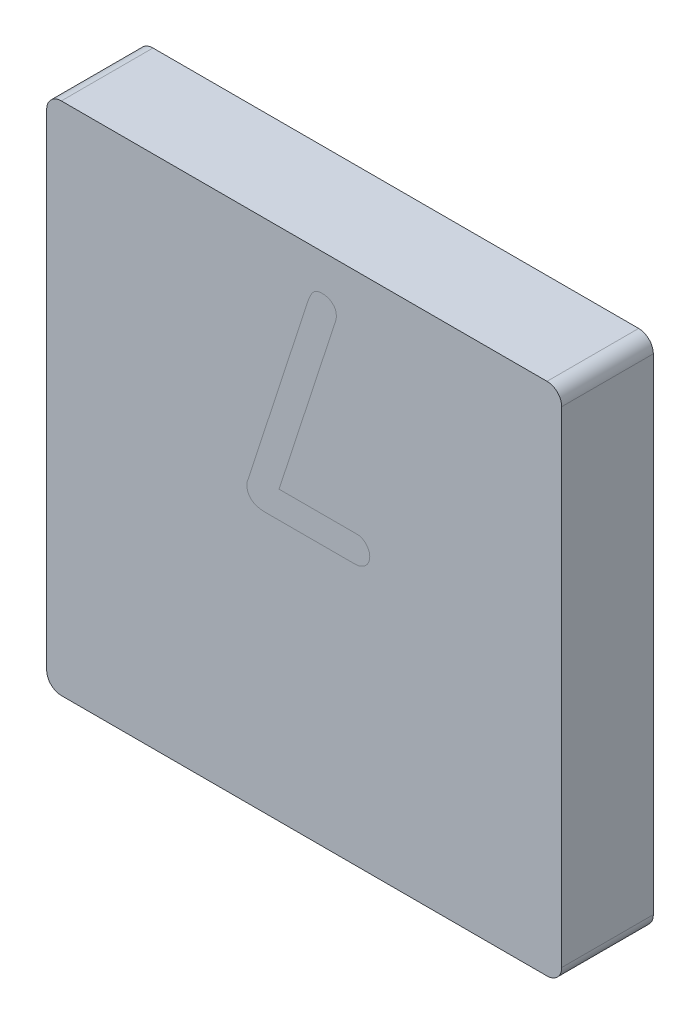
SolidWorks part; units mm, degrees
material "Nylon 101"
ref_plane "Front Plane" through (0, 0, 0) normal (0, 0, 1) x (1, 0, 0)
ref_plane "Top Plane" through (0, 0, 0) normal (0, 1, 0) x (1, 0, 0)
ref_plane "Right Plane" through (0, 0, 0) normal (1, 0, 0) x (0, 0, -1)
sketch "Sketch1" plane through (0, 0, 0) normal (0, 0, 1) x (1, 0, 0)
  line L0 (4.207, 4.715) -> (-4.207, 4.715) construction
  line L1 (4.715, -4.207) -> (4.715, 4.207) construction
  line L2 (-4.207, -4.715) -> (4.207, -4.715) construction
  line L3 (-4.715, 4.207) -> (-4.715, -4.207) construction
  line L4 (4.207, 4.715) -> (-4.207, 4.715) construction
  line L5 (4.715, -4.207) -> (4.715, 4.207) construction
  line L6 (-4.207, -4.715) -> (4.207, -4.715) construction
  line L7 (-4.715, 4.207) -> (-4.715, -4.207) construction
  line L8 (4.207, 4.461) -> (-4.207, 4.461)
  line L9 (-4.461, 4.207) -> (-4.461, -4.207)
  line L10 (-4.207, -4.461) -> (4.207, -4.461)
  line L11 (4.461, -4.207) -> (4.461, 4.207)
  arc A0 (4.715, 4.207) -> (4.207, 4.715) centre (4.207, 4.207) ccw construction
  arc A1 (4.207, -4.715) -> (4.715, -4.207) centre (4.207, -4.207) ccw construction
  arc A2 (-4.715, -4.207) -> (-4.207, -4.715) centre (-4.207, -4.207) ccw construction
  arc A3 (-4.207, 4.715) -> (-4.715, 4.207) centre (-4.207, 4.207) ccw construction
  arc A4 (4.715, 4.207) -> (4.207, 4.715) centre (4.207, 4.207) ccw construction
  arc A5 (4.207, -4.715) -> (4.715, -4.207) centre (4.207, -4.207) ccw construction
  arc A6 (-4.715, -4.207) -> (-4.207, -4.715) centre (-4.207, -4.207) ccw construction
  arc A7 (-4.207, 4.715) -> (-4.715, 4.207) centre (-4.207, 4.207) ccw construction
  arc A8 (-4.207, 4.461) -> (-4.461, 4.207) centre (-4.207, 4.207) ccw
  arc A9 (-4.461, -4.207) -> (-4.207, -4.461) centre (-4.207, -4.207) ccw
  arc A10 (4.207, -4.461) -> (4.461, -4.207) centre (4.207, -4.207) ccw
  arc A11 (4.461, 4.207) -> (4.207, 4.461) centre (4.207, 4.207) ccw
  dimension "D1" = 0.254
extrude "Boss-Extrude1" add sketch "Sketch1" along normal blind 1.5875
sketch "Sketch2" plane through (0, 0, 1.5875) normal (0, 0, 1) x (1, 0, 0)
  line L0 (4.461, 3.8355) -> (-4.461, 3.8355) construction
  line L1 (4.461, -4.207) -> (4.461, 4.207) construction
  line L2 (-4.461, 4.207) -> (-4.461, -4.207) construction
  text T0 "7" font "GordonURWMed" height in points 16
sketch "Sketch4" plane through (0, 0, 1.5875) normal (0, 0, 1) x (1, 0, 0)
  line L0 (4.461, -0.7785) -> (-4.461, -0.7785) construction
  line L1 (4.461, -4.207) -> (4.461, 4.207) construction
  line L2 (-4.461, 4.207) -> (-4.461, -4.207) construction
  text T0 "N" font "GordonURWMed" height in points 12
wrap "Direction" [suppressed] sketch "Sketch4" source sketch "Sketch4"
split line "Number"
sketch "Sketch5" [suppressed] plane through (0, 0, 1.5875) normal (0, 0, 1) x (1, 0, 0)
  line L0 (4.461, 0) -> (-4.461, 0) construction
  line L1 (4.461, -4.207) -> (4.461, 4.207) construction
  line L2 (-4.461, 4.207) -> (-4.461, -4.207) construction
  line L3 (4.461, 1.651) -> (-4.461, 1.651) construction
  text T0 "CLR" font "GordonURWMed" height in points 14
  dimension "D1" = 1.651
wrap "CLR" [suppressed] sketch "Sketch5" source sketch "Sketch5"
sketch "Sketch6" [suppressed] plane through (0, 0, 1.5875) normal (0, 0, 1) x (1, 0, 0)
  line L0 (4.461, 0) -> (-4.461, 0) construction
  line L4 (4.461, 1.651) -> (-4.461, 1.651) construction
  text T0 "ENT" font "GordonURWCon" height in points 16
  dimension "D1" = 1.651
wrap "ENT" [suppressed] sketch "Sketch6" source sketch "Sketch6"
sketch "Sketch8" [suppressed] plane through (0, 0, 1.5875) normal (0, 0, 1) x (1, 0, 0)
  line L0 (4.461, 3.302) -> (-4.461, 3.302) construction
  line L3 (4.461, 0) -> (-4.461, 0) construction
  line L4 (4.461, -0.508) -> (-4.461, -0.508) construction
  text T0 "EM" font "GordonURWCon" height in points 14
  text T1 "CON" font "GordonURWCon" height in points 14
  point P13 (0, 0)
  dimension "D1" = 3.302
  dimension "D2" = 0.508
wrap "EMCON" [suppressed] sketch "Sketch8" source sketch "Sketch8"
sketch "Sketch9" [suppressed] plane through (0, 0, 0) normal (0, 0, 1) x (1, 0, 0)
  line L0 (4.461, 3.302) -> (-4.461, 3.302) construction
  line L3 (4.461, 0) -> (-4.461, 0) construction
  line L4 (4.461, -0.508) -> (-4.461, -0.508) construction
  text T0 "ON" font "GordonURWCon" height in points 14
  text T1 "OFF" font "GordonURWCon" height in points 14
  point P13 (0, 0)
  dimension "D1" = 3.302
  dimension "D2" = 0.508
wrap "ON-OFF" [suppressed] sketch "Sketch9" source sketch "Sketch9" thickness 0.0762 parameters "D1"=0.0762
sketch "Sketch10" [suppressed] plane through (0, 0, 0) normal (0, 0, 1) x (1, 0, 0)
  line L0 (4.461, 0) -> (-4.461, 0) construction
  line L4 (4.461, 1.651) -> (-4.461, 1.651) construction
  text T0 "IFF" font "GordonURWCon" height in points 16
  dimension "D1" = 1.651
wrap "LEGEND" [suppressed] sketch "Sketch10" source sketch "Sketch10" thickness 0.0762 parameters "D1"=0.0762
sketch "Sketch11" [suppressed] plane through (0, 0, 1.5875) normal (0, 0, 1) x (1, 0, 0)
  spline S0 degree 3 poles (0.4333, 2.1341) (0.15, 2.1032) (-0.1198, 2.088) (-0.4121, 2.1993) (-0.5959, 2.4579) (-0.6685, 2.7897) (-0.5423, 3.1163) (-0.3233, 3.3286) (-0.0755, 3.3609) (0.1283, 3.3738) (0.3391, 3.3596) (0.5236, 3.2792) (0.6786, 3.1258) (0.7786, 2.9088) (0.8035, 2.6123) (0.682, 2.313) (0.4333, 2.1341) (0.15, 2.1032) (-0.1198, 2.088) knots -0.201217 -0.119698 -0.046549 0 0.077824 0.141317 0.20865 0.291476 0.367822 0.445307 0.489891 0.538926 0.589041 0.636005 0.676198 0.739165 0.798783 0.880302 0.953451 1 1.077824 1.141317 1.20865 only from (0.1949, 2.1094) to (0.1949, 2.1094)
split line "Split Line1" [suppressed]
